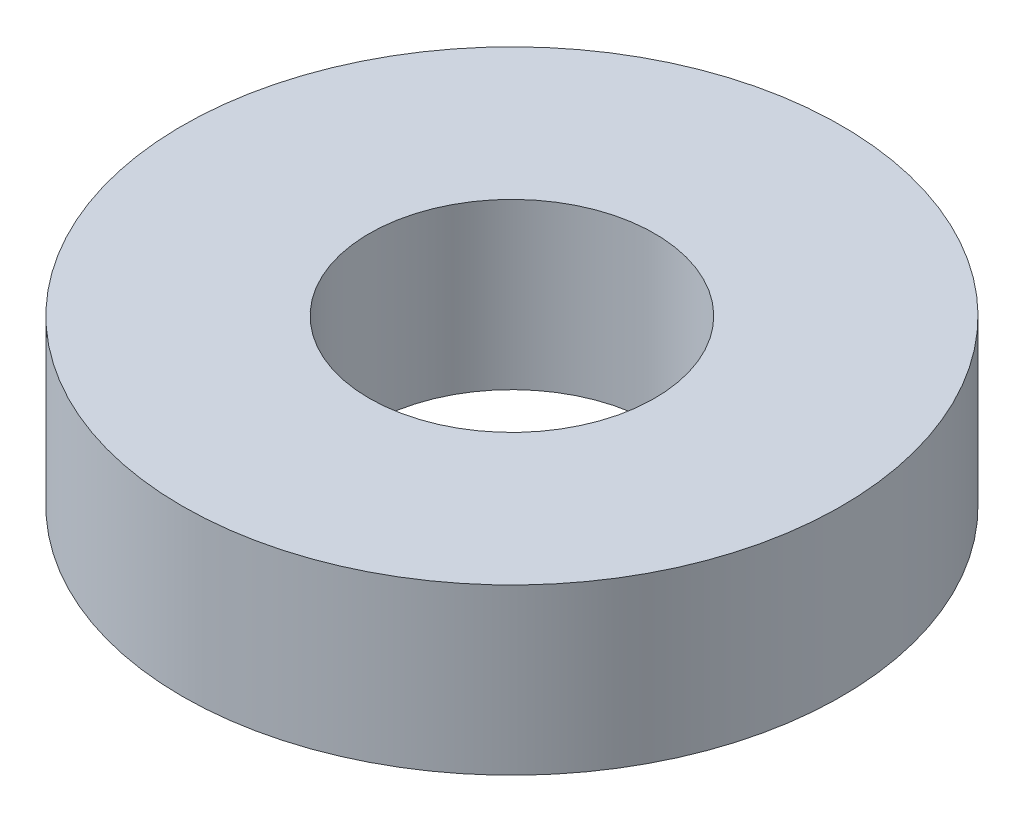
SolidWorks part; units mm, degrees
ref_plane "Front Plane" through (0, 0, 0) normal (0, 0, 1) x (1, 0, 0)
ref_plane "Top Plane" through (0, 0, 0) normal (0, 1, 0) x (1, 0, 0)
ref_plane "Right Plane" through (0, 0, 0) normal (1, 0, 0) x (0, 0, -1)
sketch "Sketch1" plane through (0, 0, 0) normal (0, 1, 0) x (1, 0, 0)
  circle A0 centre (0, 0) radius 25.4
  dimension "D1" = 50.8
extrude "Boss-Extrude1" add sketch "Sketch1" along normal blind 12.7
sketch "Sketch4" plane through (0, 12.7, 0) normal (0, 1, 0) x (1, 0, 0)
  circle A1 centre (0, 0) radius 11
extrude "Cut-Extrude3" cut sketch "Sketch4" against normal blind 60
